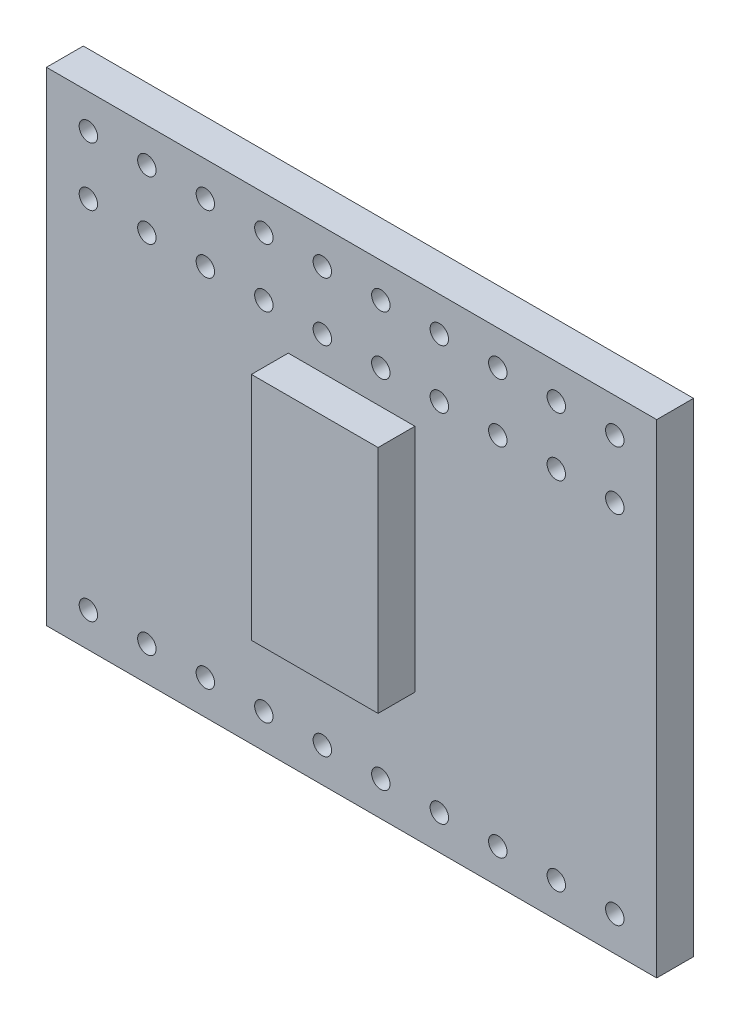
SolidWorks part; units mm, degrees
material "ABS"
ref_plane "TOP" through (0, 0, 0) normal (0, 0, 1) x (1, 0, 0)
ref_plane "FRONT" through (0, 0, 0) normal (0, 1, 0) x (1, 0, 0)
ref_plane "RIGHT" through (0, 0, 0) normal (1, 0, 0) x (0, 0, -1)
sketch "Эскиз1" plane through (0, 0, 0) normal (0, 0, 1) x (1, 0, 0)
  line L0 (-11.43, -9) -> (11.43, -9) construction
  line L1 (-13.25, 10.5) -> (13.25, 10.5)
  line L2 (-13.25, 10.5) -> (-13.25, -10.5)
  line L3 (-13.25, -10.5) -> (13.25, -10.5)
  line L4 (13.25, 10.5) -> (13.25, -10.5)
  line L5 (0, -10.5) -> (0, 10.5) construction
  line L6 (-13.25, 0) -> (13.25, 0) construction
  line L7 (-11.43, 9) -> (11.43, 9) construction
  line L8 (-11.43, 6.46) -> (11.43, 6.46) construction
  line L9 (-11.43, 9) -> (-11.43, -9) construction
  line L10 (11.43, 9) -> (11.43, -9) construction
  circle A0 centre (-11.43, -9) radius 0.4
  circle A1 centre (-8.89, -9) radius 0.4
  circle A2 centre (-6.35, -9) radius 0.4
  circle A3 centre (-3.81, -9) radius 0.4
  circle A4 centre (-1.27, -9) radius 0.4
  circle A5 centre (1.27, -9) radius 0.4
  circle A6 centre (3.81, -9) radius 0.4
  circle A7 centre (6.35, -9) radius 0.4
  circle A8 centre (8.89, -9) radius 0.4
  circle A9 centre (11.43, -9) radius 0.4
  circle A10 centre (-11.43, 9) radius 0.4
  circle A11 centre (-8.89, 9) radius 0.4
  circle A12 centre (-6.35, 9) radius 0.4
  circle A13 centre (-3.81, 9) radius 0.4
  circle A14 centre (-1.27, 9) radius 0.4
  circle A15 centre (1.27, 9) radius 0.4
  circle A16 centre (3.81, 9) radius 0.4
  circle A17 centre (6.35, 9) radius 0.4
  circle A18 centre (8.89, 9) radius 0.4
  circle A19 centre (11.43, 9) radius 0.4
  circle A20 centre (-8.89, 6.46) radius 0.4
  circle A21 centre (-6.35, 6.46) radius 0.4
  circle A22 centre (-3.81, 6.46) radius 0.4
  circle A23 centre (-1.27, 6.46) radius 0.4
  circle A24 centre (1.27, 6.46) radius 0.4
  circle A25 centre (3.81, 6.46) radius 0.4
  circle A26 centre (6.35, 6.46) radius 0.4
  circle A27 centre (8.89, 6.46) radius 0.4
  circle A28 centre (11.43, 6.46) radius 0.4
  circle A29 centre (-11.43, 6.46) radius 0.4
  point P28 (0, 0)
  point P60 (0, 0)
  point P72 (0, 9)
  dimension "D3" = 0.8
  dimension "D5" = 10
  dimension "D9" = 2.54
  dimension "D1" = 21
  dimension "D2" = 26.5
  dimension "D7" = 2.54
  dimension "D8" = 18
  dimension "D4" = 10
  dimension "D6" = 2
extrude "Бобышка-Вытянуть1" add sketch "Эскиз1" along normal blind 1.6
sketch "Эскиз2" plane through (0, 0, 1.6) normal (0, 0, 1) x (1, 0, 0)
  line L1 (-2.75, 5) -> (2.75, 5)
  line L2 (-2.75, 5) -> (-2.75, -5)
  line L3 (-2.75, -5) -> (2.75, -5)
  line L4 (2.75, 5) -> (2.75, -5)
  line L5 (0, -5) -> (0, 5) construction
  line L6 (-2.75, 0) -> (2.75, 0) construction
  point P76 (0, 0)
  dimension "D1" = 10
  dimension "D2" = 5.5
extrude "Бобышка-Вытянуть2" add sketch "Эскиз2" along normal blind 1.6
